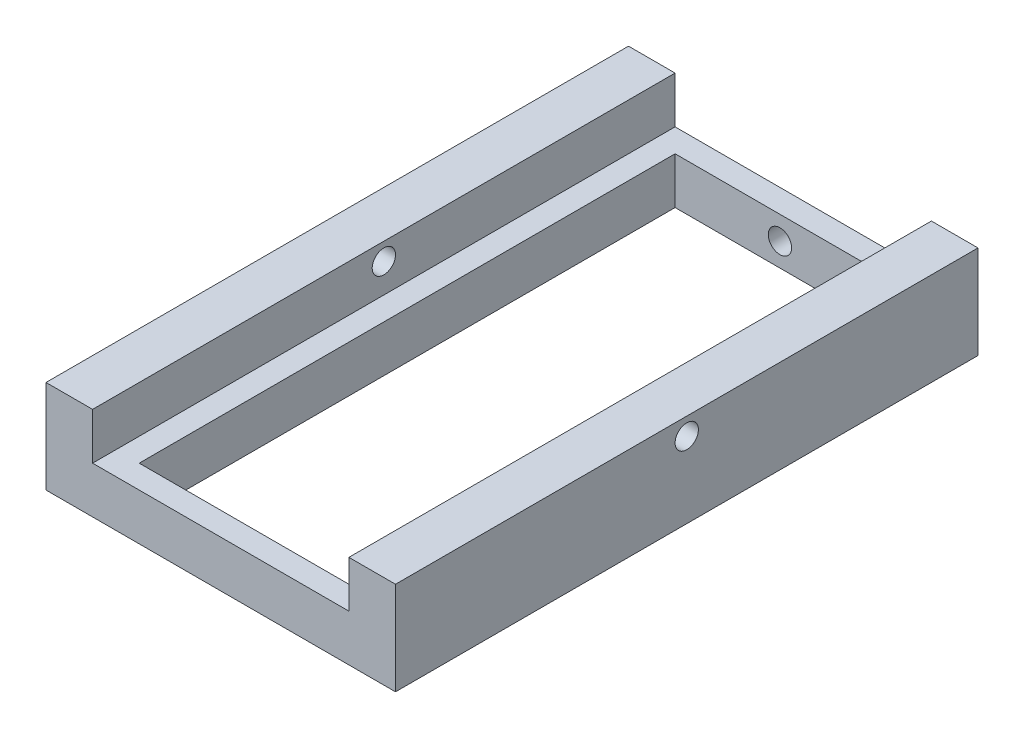
SolidWorks part; units mm, degrees
ref_plane "Front Plane" through (0, 0, 0) normal (0, 0, 1) x (1, 0, 0)
ref_plane "Top Plane" through (0, 0, 0) normal (0, 1, 0) x (1, 0, 0)
ref_plane "Right Plane" through (0, 0, 0) normal (1, 0, 0) x (0, 0, -1)
sketch "Sketch1" plane through (0, 0, 0) normal (0, 0, 1) x (1, 0, 0)
  line L1 (-110, 10) -> (110, 10)
  line L2 (-150, 10) -> (-150, -30)
  line L3 (-150, -30) -> (150, -30)
  line L4 (150, 10) -> (150, -30)
  line L5 (0, 0) -> (150, -30) construction
  line L6 (-150, -30) -> (0, 0) construction
  line L8 (150, 10) -> (150, 50)
  line L9 (150, 50) -> (110, 50)
  line L10 (110, 10) -> (110, 50)
  line L12 (-150, 10) -> (-150, 50)
  line L13 (-150, 50) -> (-110, 50)
  line L14 (-110, 10) -> (-110, 50)
  point P0 (0, 0)
  dimension "D1" = 40
  dimension "D2" = 300
  dimension "D3" = 40
  dimension "D4" = 40
  dimension "D5" = 40
  dimension "D6" = 40
  dimension "D7" = 40
extrude "Boss-Extrude1" add sketch "Sketch1" along normal mid plane 500 contours L1 L10 L9 L8 L4 L3 L2 L12 L13 L14
sketch "Sketch2" plane through (0, 10, 0) normal (0, 1, 0) x (1, 0, 0)
  line L0 (-110, -250) -> (110, -250) construction
  line L1 (-90, 230) -> (90, 230)
  line L2 (-90, 230) -> (-90, -230)
  line L3 (-90, -230) -> (90, -230)
  line L4 (90, 230) -> (90, -230)
  point P4 (0, 230)
  dimension "D1" = 180
  dimension "D2" = 460
  dimension "D3" = 20
extrude "Cut-Extrude1" cut sketch "Sketch2" against normal through all
sketch "Sketch5" plane through (0, 0, 230) normal (0, 0, -1) x (-1, 0, 0)
  line L0 (110, 10) -> (-110, 10) construction
  circle A0 centre (0, -10) radius 10
  dimension "D1" = 20
  dimension "D2" = 20
extrude "Cut-Extrude5" cut sketch "Sketch5" against normal blind 15 contours A0
sketch "Sketch6" plane through (0, 0, -250) normal (0, 0, -1) x (-1, 0, 0)
  circle A1 centre (0, -10) radius 10
  circle A2 centre (0, -10) radius 10
  dimension "D2" = 0
extrude "Cut-Extrude6" cut sketch "Sketch6" against normal blind 20
sketch "Sketch7" plane through (-150, 0, 0) normal (-1, 0, 0) x (0, 0, 1)
  line L0 (250, 50) -> (-250, 50) construction
  circle A0 centre (0, 35) radius 10
  dimension "D1" = 15
  dimension "D2" = 20
extrude "Cut-Extrude7" cut sketch "Sketch7" against normal up to surface (300 mm away) up to face at (150, 10, 0)
